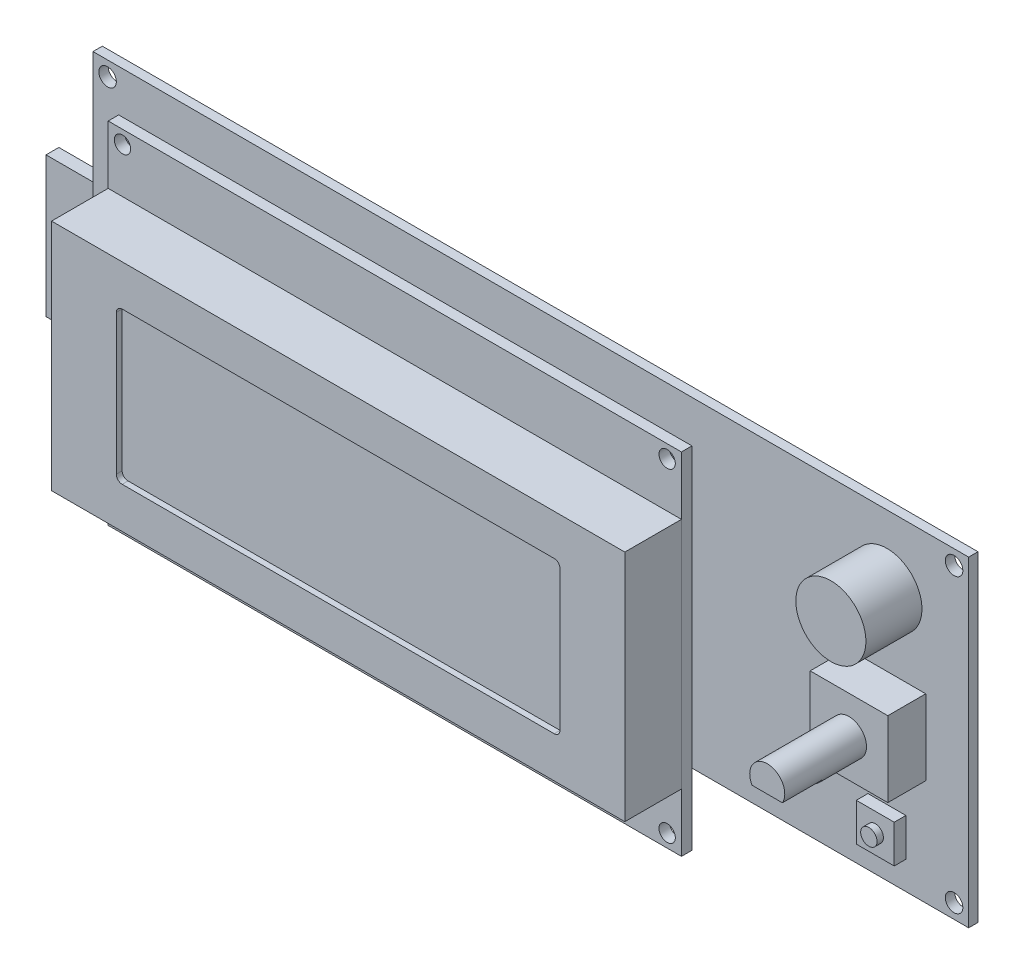
SolidWorks part; units mm, degrees
ref_plane "Front Plane" through (0, 0, 0) normal (0, 0, 1) x (1, 0, 0)
ref_plane "Top Plane" through (0, 0, 0) normal (0, 1, 0) x (1, 0, 0)
ref_plane "Right Plane" through (0, 0, 0) normal (1, 0, 0) x (0, 0, -1)
sketch "Sketch1" plane through (0, 0, 0) normal (0, 0, 1) x (1, 0, 0)
  line L1 (-75, -27.5) -> (75, -27.5)
  line L2 (-75, -27.5) -> (-75, 27.5)
  line L3 (-75, 27.5) -> (75, 27.5)
  line L4 (75, -27.5) -> (75, 27.5)
  line L5 (-75, -27.5) -> (75, 27.5) construction
  line L6 (-75, 27.5) -> (75, -27.5) construction
  point P0 (0, 0)
  dimension "D1" = 150
  dimension "D2" = 55
extrude "PCB" add sketch "Sketch1" against normal blind 1.6
hole_wizard "Ø3.0 (3) Diameter Hole1" positions "Sketch3" profile "Sketch2" hole size "Ø3.0" standard "ANSI Metric"
sketch "Sketch3" plane through (0, 0, 0) normal (0, 0, 1) x (1, 0, 0)
  line L1 (72.5, -25) -> (-72.5, -25)
  line L2 (72.5, -25) -> (72.5, 25)
  line L3 (72.5, 25) -> (-72.5, 25)
  line L4 (-72.5, -25) -> (-72.5, 25)
  line L5 (72.5, -25) -> (-72.5, 25) construction
  line L6 (72.5, 25) -> (-72.5, -25) construction
  line L7 (75, 27.5) -> (-75, 27.5) construction
  line L8 (-75, 27.5) -> (-75, -27.5) construction
  point P0 (-72.5, 25)
  point P2 (72.5, 25)
  point P4 (72.5, -25)
  point P6 (-72.5, -25)
  dimension "D1" = 2.5
  dimension "D2" = 2.5
sketch "Sketch2" plane through (-72.5, 25, 0) normal (1, 0, 0) x (0, -1, 0)
  line L0 (0, 0) -> (0, 4.9013)
  line L1 (0, 4.9013) -> (1.5, 4)
  line L2 (1.5, 4) -> (1.5, 0)
  line L5 (1.5, 0) -> (0, 0)
  line L10 (0, 4.9013) -> (-1.5, 4) construction
  line L11 (0, -6.35) -> (0, 107.95) construction
  dimension "Hole Dia." = 3
  dimension "Hole Depth" = 4
  dimension "Drill Angle" = 118
sketch "Sketch4" plane through (0, 0, -1.6) normal (0, 0, -1) x (-1, 0, 0)
  line L0 (75, -27.5) -> (-75, -27.5) construction
  line L1 (-14.2, 5) -> (6.1, 5)
  line L2 (-14.2, 5) -> (-14.2, -3.8)
  line L3 (-14.2, -3.8) -> (6.1, -3.8)
  line L4 (6.1, 5) -> (6.1, -3.8)
  line L5 (-75, -27.5) -> (-75, 27.5) construction
  dimension "D1" = 20.3
  dimension "D2" = 8.8
  dimension "D3" = 32.5
  dimension "D4" = 60.8
extrude "IDC conn" add sketch "Sketch4" along normal blind 17.5
pattern_linear "LPattern1" count 2 spacing 22.86 along (-1, 0, 0) of "IDC conn"
sketch "Sketch5" plane through (0, 0, -1.6) normal (0, 0, -1) x (-1, 0, 0)
  line L0 (75, 27.5) -> (75, -27.5) construction
  line L1 (75, -19.3) -> (49.3, -19.3)
  line L2 (75, -19.3) -> (75, 7.3)
  line L3 (75, 7.3) -> (49.3, 7.3)
  line L4 (49.3, -19.3) -> (49.3, 7.3)
  line L5 (75, -27.5) -> (-75, -27.5) construction
  dimension "D1" = 26.6
  dimension "D2" = 25.7
  dimension "D3" = 8.2
extrude "SD socket" add sketch "Sketch5" along normal blind 3.3 separate body
sketch "Sketch6" plane through (-75, 0, 0) normal (-1, 0, 0) x (0, 0, 1)
  line L0 (-4.35, 6) -> (-2.15, -18) construction
  line L1 (-4.35, 6) -> (-2.15, 6)
  line L2 (-4.35, 6) -> (-4.35, -18)
  line L3 (-4.35, -18) -> (-2.15, -18)
  line L4 (-2.15, 6) -> (-2.15, -18)
  line L5 (-1.6, 7.3) -> (-4.9, -19.3) construction
  point P8 (-3.25, -6)
  point P9 (-3.25, -6)
  dimension "D1" = 24
  dimension "D2" = 2.2
extrude "SD card" add sketch "Sketch6" along normal blind 10.2
sketch "Sketch7" plane through (0, 0, -1.6) normal (0, 0, -1) x (-1, 0, 0)
  line L0 (-75, 27.5) -> (75, 27.5) construction
  line L1 (75, 27.5) -> (75, 7.3) construction
  line L2 (50.95, 12.85) -> (51.7, 12.85)
  line L3 (50.45, 12.1) -> (50.95, 12.1)
  line L4 (50.45, 12.1) -> (50.45, 12.85)
  line L5 (50.45, 14.1) -> (50.95, 14.1)
  line L6 (50.95, 12.1) -> (50.95, 12.85)
  line L7 (50.45, 12.1) -> (50.95, 14.1) construction
  line L8 (50.45, 14.1) -> (50.95, 12.1) construction
  line L9 (49.7, 12.85) -> (50.45, 12.85)
  line L10 (49.7, 12.85) -> (49.7, 13.35)
  line L11 (49.7, 13.35) -> (50.45, 13.35)
  line L12 (51.7, 12.85) -> (51.7, 13.35)
  line L13 (49.7, 12.85) -> (51.7, 13.35) construction
  line L14 (49.7, 13.35) -> (51.7, 12.85) construction
  line L15 (50.95, 13.35) -> (50.95, 14.1)
  line L16 (50.95, 13.35) -> (51.7, 13.35)
  line L17 (50.45, 13.35) -> (50.45, 14.1)
  circle A0 centre (50.7, 13.1) radius 1.75
  point P10 (50.7, 13.1)
  dimension "D1" = 3.5
  dimension "D2" = 14.4
  dimension "D3" = 24.3
  dimension "D4" = 0.5
  dimension "D5" = 2
extrude "Contrast pot" add sketch "Sketch7" along normal blind 2.5
sketch "Sketch8" plane through (0, 0, -1.6) normal (0, 0, -1) x (-1, 0, 0)
  line L0 (-3.8, 11.0707) -> (-3.8, 14.7293)
  line L1 (-75, 27.5) -> (75, 27.5) construction
  line L2 (-75, -27.5) -> (-75, 27.5) construction
  arc A0 (-3.8, 14.7293) -> (-3.8, 11.0707) centre (-5.235, 12.9) ccw
  dimension "D1" = 2.325
  dimension "D2" = 3.76
  dimension "D3" = 14.6
  dimension "D4" = 71.2
extrude "2N3901" add sketch "Sketch8" along normal blind 7
ref_plane "Plane1" through (0, 0, 4) normal (0, 0, 1) x (1, 0, 0)
sketch "Sketch9" plane through (0, 0, 4) normal (0, 0, 1) x (1, 0, 0)
  line L0 (-75, 27.5) -> (-75, -27.5) construction
  line L1 (-66.6, 24.3) -> (31.6, 24.3)
  line L2 (-66.6, 24.3) -> (-66.6, -35.7)
  line L3 (-66.6, -35.7) -> (31.6, -35.7)
  line L4 (31.6, 24.3) -> (31.6, -35.7)
  line L5 (75, 27.5) -> (-75, 27.5) construction
  dimension "D1" = 60
  dimension "D2" = 98.2
  dimension "D3" = 8.4
  dimension "D4" = 3.2
extrude "LCD PCB" add sketch "Sketch9" along normal blind 1.8 separate body
sketch "Sketch10" plane through (0, 0, 5.8) normal (0, 0, 1) x (1, 0, 0)
  line L0 (-66.6, 24.3) -> (-66.6, -35.7) construction
  line L1 (-66.6, 14.3) -> (31.6, 14.3)
  line L2 (-66.6, 14.3) -> (-66.6, -25.7)
  line L3 (-66.6, -25.7) -> (31.6, -25.7)
  line L4 (31.6, 14.3) -> (31.6, -25.7)
  line L5 (31.6, -35.7) -> (31.6, 24.3) construction
  point P8 (-66.6, -5.7)
  dimension "D1" = 40
extrude "LCD housing" add sketch "Sketch10" along normal blind 9.7 separate body
sketch "Sketch11" plane through (0, 0, 15.5) normal (0, 0, 1) x (1, 0, 0)
  line L0 (-66.6, -25.7) -> (31.6, 14.3) construction
  line L2 (20.5, -18.7) -> (-55.5, -18.7)
  line L3 (20.5, -18.7) -> (20.5, 7.3)
  line L4 (20.5, 7.3) -> (-55.5, 7.3)
  line L5 (-55.5, -18.7) -> (-55.5, 7.3)
  line L6 (20.5, -18.7) -> (-55.5, 7.3) construction
  line L7 (20.5, 7.3) -> (-55.5, -18.7) construction
  point P2 (-17.5, -5.7)
  dimension "D1" = 76
  dimension "D2" = 26
extrude "Cut-Extrude1" cut sketch "Sketch11" against normal blind 1
fillet "Fillet1" radius 1 4 edges at (-55.5, -18.7, 15) (-55.5, 7.3, 15) (20.5, -18.7, 15) (20.5, 7.3, 15)
hole_wizard "Ø2.8 (2.8) Diameter Hole1" positions "Sketch13" profile "Sketch12" hole size "Ø2.8" standard "ANSI Metric"
sketch "Sketch13" plane through (0, 0, 5.8) normal (0, 0, 1) x (1, 0, 0)
  line L1 (29.15, -33.45) -> (-64.15, -33.45)
  line L2 (29.15, -33.45) -> (29.15, 22.05)
  line L3 (29.15, 22.05) -> (-64.15, 22.05)
  line L4 (-64.15, -33.45) -> (-64.15, 22.05)
  line L5 (29.15, -33.45) -> (-64.15, 22.05) construction
  line L6 (29.15, 22.05) -> (-64.15, -33.45) construction
  line L7 (-17.5, -35.7) -> (-17.5, 24.3) construction
  line L8 (-66.6, -35.7) -> (31.6, -35.7) construction
  line L9 (31.6, 24.3) -> (-66.6, 24.3) construction
  point P0 (-64.15, 22.05)
  point P2 (29.15, 22.05)
  point P4 (29.15, -33.45)
  point P6 (-64.15, -33.45)
  point P190 (-17.5, -5.7)
  dimension "D1" = 55.5
  dimension "D2" = 93.3
sketch "Sketch12" plane through (-64.15, 22.05, 5.8) normal (1, 0, 0) x (0, -1, 0)
  line L0 (0, 0) -> (0, 4.8412)
  line L1 (0, 4.8412) -> (1.4, 4)
  line L2 (1.4, 4) -> (1.4, 0)
  line L5 (1.4, 0) -> (0, 0)
  line L10 (0, 4.8412) -> (-1.4, 4) construction
  line L11 (0, -6.35) -> (0, 107.95) construction
  dimension "Hole Dia." = 2.8
  dimension "Hole Depth" = 4
  dimension "Drill Angle" = 118
sketch "Sketch14" plane through (0, 0, 0) normal (0, 0, 1) x (1, 0, 0)
  line L0 (75, 27.5) -> (-75, 27.5) construction
  line L1 (75, -27.5) -> (75, 27.5) construction
  circle A0 centre (61, 15.8) radius 6
  dimension "D1" = 12
  dimension "D2" = 11.7
  dimension "D3" = 14
extrude "buzzer" add sketch "Sketch14" along normal blind 9.6
sketch "Sketch15" plane through (0, 0, 0) normal (0, 0, 1) x (1, 0, 0)
  line L0 (61, 15.8) -> (61, -2.9) construction
  line L1 (54.35, -9.35) -> (67.65, -9.35)
  line L2 (54.35, -9.35) -> (54.35, 3.55)
  line L3 (54.35, 3.55) -> (67.65, 3.55)
  line L4 (67.65, -9.35) -> (67.65, 3.55)
  line L5 (54.35, -9.35) -> (67.65, 3.55) construction
  line L6 (54.35, 3.55) -> (67.65, -9.35) construction
  line L7 (75, 27.5) -> (-75, 27.5) construction
  point P0 (61, -2.9)
  dimension "D1" = 13.3
  dimension "D2" = 12.9
  dimension "D3" = 30.4
extrude "enc body" add sketch "Sketch15" along normal blind 6.5
sketch "Sketch16" plane through (0, 0, 6.5) normal (0, 0, 1) x (1, 0, 0)
  line L0 (54.35, -9.35) -> (67.65, 3.55) construction
  circle A0 centre (61, -2.9) radius 3
  dimension "D1" = 3
extrude "enc shaft" add sketch "Sketch16" along normal blind 14
sketch "Sketch17" plane through (0, 0, 20.5) normal (0, 0, 1) x (1, 0, 0)
  line L1 (58.4019, -4.4) -> (63.5981, -4.4)
  line L2 (58.4019, -4.4) -> (58.4019, -5.9)
  line L3 (58.4019, -5.9) -> (63.5981, -5.9)
  line L4 (63.5981, -4.4) -> (63.5981, -5.9)
  circle A0 centre (61, -2.9) radius 3 construction
  dimension "D1" = 4.5
extrude "enc shaft flat" cut sketch "Sketch17" against normal blind 6.8
sketch "Sketch18" plane through (0, 0, 0) normal (0, 0, 1) x (1, 0, 0)
  line L0 (61, -19.45) -> (61, 15.8) construction
  line L1 (57.75, -22.7) -> (64.25, -22.7)
  line L2 (57.75, -22.7) -> (57.75, -16.2)
  line L3 (57.75, -16.2) -> (64.25, -16.2)
  line L4 (64.25, -22.7) -> (64.25, -16.2)
  line L5 (57.75, -22.7) -> (64.25, -16.2) construction
  line L6 (57.75, -16.2) -> (64.25, -22.7) construction
  line L7 (-75, -27.5) -> (75, -27.5) construction
  point P0 (61, -19.45)
  dimension "D1" = 6.5
  dimension "D2" = 4.8
extrude "e-stop sw body" add sketch "Sketch18" along normal blind 2
sketch "Sketch19" plane through (0, 0, 2) normal (0, 0, 1) x (1, 0, 0)
  line L0 (57.75, -22.7) -> (64.25, -16.2) construction
  circle A0 centre (61, -19.45) radius 1.4
  dimension "D1" = 2.8
extrude "e-stop sw button" add sketch "Sketch19" along normal blind 1.1
